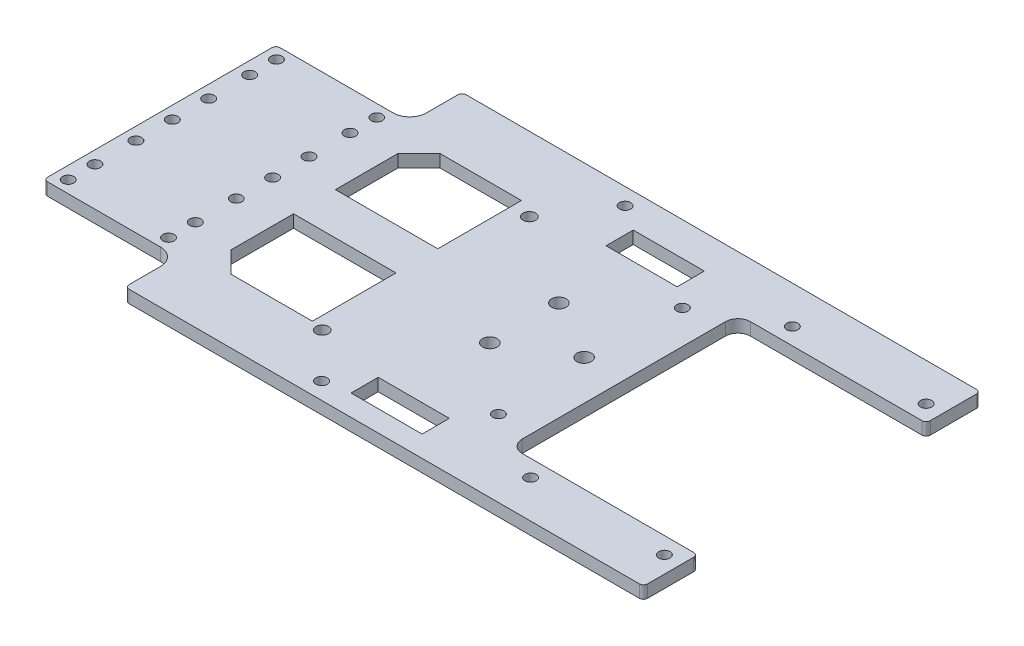
SolidWorks part; units mm, degrees
material "Acrylic (Medium-high impact)"
ref_plane "Front Plane" through (0, 0, 0) normal (0, 0, 1) x (1, 0, 0)
ref_plane "Top Plane" through (0, 0, 0) normal (0, 1, 0) x (1, 0, 0)
ref_plane "Right Plane" through (0, 0, 0) normal (1, 0, 0) x (0, 0, -1)
sketch "Sketch1" plane through (0, 0, 0) normal (0, 1, 0) x (1, 0, 0)
  line L0 (0, 27.8) -> (0, -27.8)
  line L1 (0, 27.8) -> (32, 27.8)
  line L2 (0, -27.8) -> (32, -27.8)
  line L3 (156, 40.3) -> (156, -40.3) construction
  line L4 (156, 40.3) -> (156, 27.3)
  line L5 (156, 27.3) -> (111, 27.3)
  line L6 (111, 27.3) -> (111, -27.3)
  line L7 (111, -27.3) -> (156, -27.3)
  line L8 (156, -27.3) -> (156, -40.3)
  line L9 (156, -40.3) -> (32, -40.3)
  line L10 (156, 40.3) -> (32, 40.3)
  line L13 (32, -27.8) -> (32, -40.3)
  line L14 (32, 40.3) -> (32, 27.8)
  point P2 (0, 0)
  point P3 (156, 0)
  point P7 (111, 0)
  dimension "D1" = 55.6
  dimension "D2" = 32
  dimension "D3" = 156
  dimension "D4" = 80.6
  dimension "D5" = 13
  dimension "D6" = 45
extrude "Boss-Extrude1" add sketch "Sketch1" along normal blind 3 contours L0 L2 L13 L9 L8 L7 L6 L5 L4 L10 L14 L1
sketch "Sketch2" plane through (0, 3, 0) normal (0, 1, 0) x (1, 0, 0)
  line L0 (3, 8.7) -> (3, -8.7) construction
  line L1 (3, 24.9) -> (3, 8.7) construction
  line L2 (3, -8.7) -> (3, -24.9) construction
  line L3 (0, 27.8) -> (0, -27.8) construction
  circle A0 centre (3, 8.7) radius 1.35
  circle A1 centre (3, 24.9) radius 1.35
  circle A2 centre (3, -8.7) radius 1.35
  circle A3 centre (3, -24.9) radius 1.35
  point P8 (3, 0)
  dimension "D4" = 2.7
  dimension "D1" = 17.4
  dimension "D2" = 16.2
  dimension "D3" = 16.2
  dimension "D5" = 3
extrude "Cut-Extrude1" cut sketch "Sketch2" against normal through all
sketch "Sketch4" plane through (0, 3, 0) normal (0, 1, 0) x (1, 0, 0)
  line L1 (75, 36.3) -> (75, -36.3) construction
  line L2 (156, -27.3) -> (156, -40.3) construction
  circle A0 centre (75, -36.3) radius 1.35
  circle A1 centre (75, 36.3) radius 1.35
  point P4 (75, 0)
  dimension "D2" = 2.7
  dimension "D1" = 81
  dimension "D3" = 72.6
sketch "Sketch5" plane through (0, 3, 0) normal (0, 1, 0) x (1, 0, 0)
  line L0 (103, 22) -> (103, -22) construction
  line L1 (0, 27.8) -> (0, -27.8) construction
  line L2 (103, 0) -> (0, 0) construction
  line L3 (156, -27.3) -> (156, -40.3) construction
  circle A0 centre (103, 22) radius 1.35
  circle A1 centre (103, -22) radius 1.35
  dimension "D1" = 2.7
  dimension "D2" = 44
  dimension "D3" = 53
extrude "Cut-Extrude2" cut sketch "Sketch4" against normal through all
extrude "Cut-Extrude3" cut sketch "Sketch5" against normal through all
sketch "Sketch6" plane through (0, 3, 0) normal (0, 1, 0) x (1, 0, 0)
  line L1 (120, -31.3) -> (152, -31.3) construction
  line L2 (120, -31.3) -> (120, 31.3) construction
  line L3 (120, 31.3) -> (152, 31.3) construction
  line L4 (152, -31.3) -> (152, 31.3) construction
  line L5 (156, -27.3) -> (156, -40.3) construction
  circle A0 centre (120, 31.3) radius 1.35
  circle A1 centre (152, 31.3) radius 1.35
  circle A2 centre (120, -31.3) radius 1.35
  circle A3 centre (152, -31.3) radius 1.35
  point P8 (120, 0)
  dimension "D3" = 2.7
  dimension "D1" = 62.6
  dimension "D2" = 32
  dimension "D4" = 4
extrude "Cut-Extrude4" cut sketch "Sketch6" against normal through all
fillet "Fillet1" radius 3 2 edges at (111, 1.5, 27.3) (111, 1.5, -27.3)
sketch "Sketch7" plane through (0, 3, 0) normal (0, 1, 0) x (1, 0, 0)
  line L0 (156, -27.3) -> (156, -40.3) construction
  line L1 (83.5, 10) -> (103.5, 10) construction
  line L2 (83.5, 10) -> (83.5, -10) construction
  line L3 (83.5, -10) -> (103.5, -10) construction
  line L4 (103.5, 10) -> (103.5, -10) construction
  line L5 (101.5, 0) -> (87.2106, 8.25) construction
  line L6 (87.2106, 8.25) -> (87.2106, -8.25) construction
  line L7 (87.2106, -8.25) -> (101.5, 0) construction
  line L8 (93.5, 10) -> (93.5, -10) construction
  line L9 (87.2106, 0) -> (101.5, 0) construction
  circle A0 centre (83.5, 10) radius 1.5 construction
  circle A1 centre (103.5, 10) radius 1.5 construction
  circle A2 centre (83.5, -10) radius 1.5 construction
  circle A3 centre (103.5, -10) radius 1.5 construction
  circle A4 centre (101.5, 0) radius 1.75
  circle A5 centre (87.2106, 8.25) radius 1.75
  circle A6 centre (87.2106, -8.25) radius 1.75
  point P4 (83.5, 0)
  point P10 (93.5, -10)
  point P23 (99.7514, 0.8113)
  point P26 (93.5, 0)
  dimension "D3" = 3
  dimension "D5" = 3.5
  dimension "D1" = 20
  dimension "D2" = 20
  dimension "D4" = 62.5
  dimension "D6" = 60
  dimension "D7" = 60
  dimension "D8" = 16.5
  dimension "D9" = 2
extrude "Cut-Extrude5" cut sketch "Sketch7" against normal through all
pattern_linear "LPattern1" count 2 spacing 24 along (1, 0, 0) of "Cut-Extrude1"
sketch "Sketch8" plane through (0, 3, 0) normal (0, 1, 0) x (1, 0, 0)
  line L0 (0, 27.8) -> (0, -27.8) construction
  circle A0 centre (3, 18.5) radius 1.35
  circle A1 centre (27, 18.5) radius 1.35
  circle A2 centre (3, -18.5) radius 1.35
  circle A3 centre (27, -18.5) radius 1.35
  circle A6 centre (3, 0) radius 1.35
  circle A7 centre (27, 0) radius 1.35
  point P8 (0, 0)
  point P9 (0, 0)
  point P13 (0, 0)
  dimension "D1" = 2.7
  dimension "D2" = 3
  dimension "D3" = 24
  dimension "D4" = 18.5
  dimension "D5" = 18.5
extrude "Cut-Extrude6" cut sketch "Sketch8" against normal through all
sketch "Sketch9" plane through (0, 3, 0) normal (0, 1, 0) x (1, 0, 0)
  line L0 (0, 27.8) -> (0, -27.8) construction
  line L1 (0, 27.8) -> (32, 27.8) construction
  circle A0 centre (65.8, 22.6) radius 1.5
  circle A1 centre (64.53, -25.66) radius 1.5
  dimension "D1" = 3
  dimension "D2" = 65.8
  dimension "D3" = 5.2
  dimension "D4" = 1.27
  dimension "D5" = 48.26
extrude "Cut-Extrude7" cut sketch "Sketch9" against normal through all
sketch "Sketch10" plane through (0, 3, 0) normal (0, 1, 0) x (1, 0, 0)
  line L0 (0, 27.8) -> (0, -27.8) construction
  line L3 (37, 5) -> (61.5, 5)
  line L4 (61.5, 25) -> (61.5, 5)
  line L6 (37, -5) -> (61.5, -5)
  line L8 (42, -25) -> (61.5, -25)
  line L9 (61.5, -5) -> (61.5, -25)
  line L10 (42, 25) -> (37, 20)
  line L11 (37, 20) -> (37, 5)
  line L13 (32, 40.3) -> (32, 27.8) construction
  line L14 (61.5, 25) -> (42, 25)
  line L15 (37, -5) -> (37, -20)
  line L16 (37, -20) -> (42, -25)
  point P0 (0, 0)
  point P10 (0, 0)
  dimension "D1" = 5
  dimension "D2" = 61.5
  dimension "D3" = 5
  dimension "D4" = 5
  dimension "D5" = 135
  dimension "D6" = 20
  dimension "D7" = 135
  dimension "D8" = 15
extrude "Cut-Extrude8" cut sketch "Sketch10" against normal through all
fillet "Fillet2" radius 1 8 edges at (156, 1.5, 27.3) (156, 1.5, -40.3) (156, 1.5, -27.3) (156, 1.5, 40.3) (32, 1.5, 40.3) (32, 1.5, -40.3) (0, 1.5, -27.8) (0, 1.5, 27.8)
fillet "Fillet3" radius 4 2 edges at (32, 1.5, -27.8) (32, 1.5, 27.8)
sketch "Sketch11" plane through (0, 3, 0) normal (0, 1, 0) x (1, 0, 0)
  line L1 (81, 32.25) -> (98, 32.25)
  line L2 (81, 32.25) -> (81, 25.75)
  line L3 (81, 25.75) -> (98, 25.75)
  line L4 (98, 32.25) -> (98, 25.75)
  line L5 (81, -28.75) -> (98, -28.75)
  line L6 (81, -28.75) -> (81, -35.25)
  line L7 (81, -35.25) -> (98, -35.25)
  line L8 (98, -28.75) -> (98, -35.25)
  line L9 (0, 26.8) -> (0, -26.8) construction
  line L10 (0, 0) -> (93.6805, 0) construction
  point P8 (81, -32)
  point P14 (95.2984, 28.3991)
  dimension "D1" = 81
  dimension "D2" = 6.5
  dimension "D3" = 32
  dimension "D4" = 17
  dimension "D5" = 25.75
  dimension "D6" = 6.5
extrude "Cut-Extrude9" cut sketch "Sketch11" against normal through all
